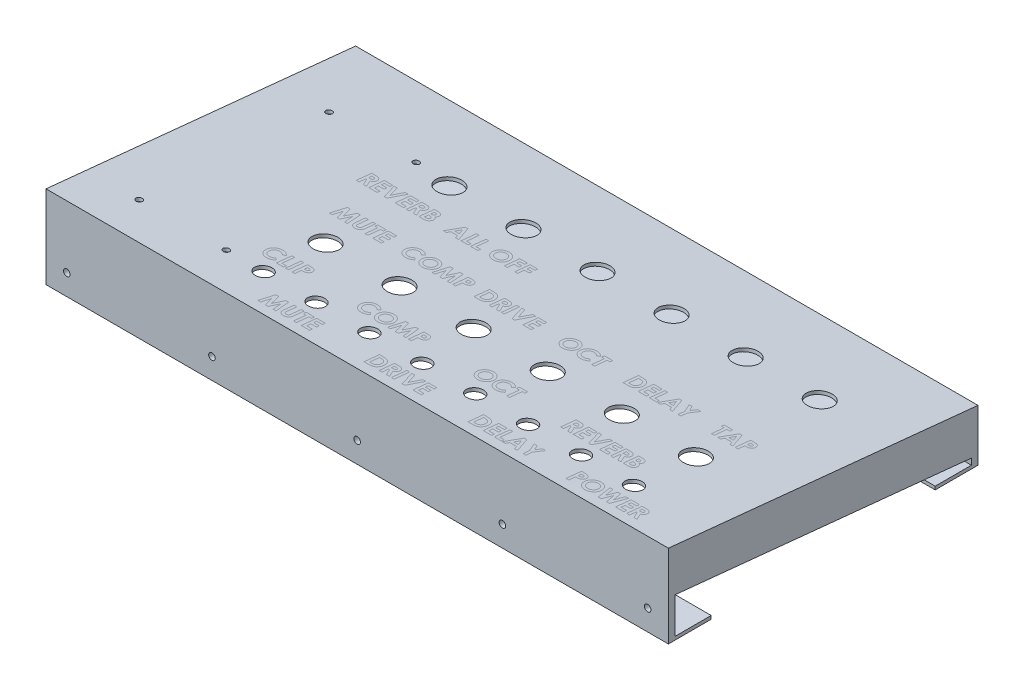
SolidWorks part; units mm, degrees
ref_plane "Plan de face" through (0, 0, 0) normal (0, 0, 1) x (1, 0, 0)
ref_plane "Plan de dessus" through (0, 0, 0) normal (0, 1, 0) x (1, 0, 0)
ref_plane "Plan de droite" through (0, 0, 0) normal (1, 0, 0) x (0, 0, -1)
sketch "Esquisse1" plane through (0, 0, 0) normal (1, 0, 0) x (0, 0, -1)
  line L0 (-26.398, -24.4282) -> (-26.398, 15.5718)
  line L1 (-26.398, 15.5718) -> (122.8501, 0.5718)
  line L2 (122.8501, 0.5718) -> (122.8501, -24.4282)
  line L3 (122.8501, -24.4282) -> (121.2626, -24.4282)
  line L4 (121.2626, -24.4282) -> (121.2626, -0.8641)
  line L5 (121.2626, -0.8641) -> (-24.8105, 13.8168)
  line L6 (-24.8105, 13.8168) -> (-24.8105, -24.4282)
  line L7 (-24.8105, -24.4282) -> (-26.398, -24.4282)
  line L8 (110.6669, 0.2008) -> (110.8256, 1.7803) construction
  dimension "D1" = 1.5875
  dimension "D2" = 40
  dimension "D3" = 25
  dimension "D4" = 150
extrude "Boss.-Extru.1" add sketch "Esquisse1" along normal blind 300
sketch "Esquisse3" plane through (0, 0, 24.8105) normal (0, 0, -1) x (-1, 0, 0)
  line L0 (-300, -24.4282) -> (-300, 13.8168) construction
  line L1 (-300, -5.3782) -> (0, -5.3782)
  line L2 (-300, -5.3782) -> (-300, -24.4282)
  line L3 (-300, -24.4282) -> (0, -24.4282)
  line L4 (0, -5.3782) -> (0, -24.4282)
  line L5 (-300, -24.4282) -> (0, -24.4282) construction
  line L6 (0, -24.4282) -> (0, 13.8168) construction
  dimension "D1" = 19.05
extrude "Boss.-Extru.2" add sketch "Esquisse3" along normal blind 1.5875
sketch "Esquisse4" plane through (0, 0, 23.223) normal (0, 0, -1) x (-1, 0, 0)
  line L0 (-300, -5.3782) -> (-300, -24.4282) construction
  line L1 (-300, -22.8407) -> (0, -22.8407)
  line L2 (-300, -22.8407) -> (-300, -24.4282)
  line L3 (-300, -24.4282) -> (0, -24.4282)
  line L4 (0, -22.8407) -> (0, -24.4282)
  line L5 (-300, -24.4282) -> (0, -24.4282) construction
  line L6 (0, -24.4282) -> (0, -5.3782) construction
  dimension "D1" = 1.5875
extrude "Boss.-Extru.3" add sketch "Esquisse4" along normal blind 17.4625
sketch "Esquisse5" plane through (0, 0, -121.2626) normal (0, 0, 1) x (1, 0, 0)
  line L0 (300, -24.4282) -> (0, -24.4282) construction
  line L1 (0, -5.3782) -> (300, -5.3782)
  line L2 (0, -5.3782) -> (0, -24.4282)
  line L3 (0, -24.4282) -> (300, -24.4282)
  line L4 (300, -5.3782) -> (300, -24.4282)
  line L5 (300, -0.8641) -> (300, -24.4282) construction
  line L6 (0, -0.8641) -> (0, -24.4282) construction
  dimension "D1" = 19.05
extrude "Boss.-Extru.4" add sketch "Esquisse5" along normal blind 1.5875
sketch "Esquisse6" plane through (0, 0, -119.6751) normal (0, 0, 1) x (1, 0, 0)
  line L0 (0, -5.3782) -> (0, -24.4282) construction
  line L1 (0, -22.8407) -> (300, -22.8407)
  line L2 (0, -22.8407) -> (0, -24.4282)
  line L3 (0, -24.4282) -> (300, -24.4282)
  line L4 (300, -22.8407) -> (300, -24.4282)
  dimension "D1" = 1.5875
extrude "Boss.-Extru.5" add sketch "Esquisse6" along normal blind 17.4625
sketch "Esquisse7" plane through (300, 0, 0) normal (1, 0, 0) x (0, 0, -1)
  line L0 (-24.8105, 13.8168) -> (-24.8105, 12.2213)
  line L1 (-24.8105, -5.3782) -> (-24.8105, 13.8168) construction
  line L2 (-24.8105, 12.2213) -> (121.2626, -2.4596)
  line L4 (121.2626, -2.4596) -> (121.2626, -0.8641)
  line L5 (121.2626, -0.8641) -> (-24.8105, 13.8168)
  dimension "D1" = 1.5875
extrude "Boss.-Extru.6" add sketch "Esquisse7" against normal blind 19.05
sketch "Esquisse8" plane through (300, 0, 0) normal (1, 0, 0) x (0, 0, -1)
  line L0 (-24.8105, 12.2213) -> (121.2626, -2.4596)
  line L1 (121.2626, -2.4596) -> (121.2626, -5.3782)
  line L2 (121.2626, -5.3782) -> (119.6751, -5.3782)
  line L3 (119.6751, -5.3782) -> (119.6751, -19.8505)
  line L4 (119.6751, -22.8407) -> (119.6751, -5.3782) construction
  line L5 (119.6751, -19.8505) -> (-24.8105, -5.3292)
  line L6 (-24.8105, -5.3782) -> (-24.8105, 12.2213) construction
  line L7 (-24.8105, -5.3292) -> (-24.8105, 12.2213)
  dimension "D1" = 17.4625
extrude "Boss.-Extru.7" add sketch "Esquisse8" against normal blind 1.5875
sketch "Esquisse9" plane through (0, 0, 0) normal (-1, 0, 0) x (0, 0, 1)
  line L0 (-121.2626, -0.8641) -> (24.8105, 13.8168)
  line L1 (24.8105, 13.8168) -> (24.8105, 12.2213)
  line L2 (24.8105, -5.3782) -> (24.8105, 13.8168) construction
  line L3 (24.8105, 12.2213) -> (-121.2626, -2.4596)
  line L4 (-121.2626, -0.8641) -> (-121.2626, -5.3782) construction
  line L5 (-121.2626, -2.4596) -> (-121.2626, -0.8641)
  dimension "D1" = 1.5875
extrude "Boss.-Extru.8" add sketch "Esquisse9" against normal blind 19.05 separate body
sketch "Esquisse11" plane through (0, 0, 0) normal (-1, 0, 0) x (0, 0, 1)
  line L0 (-121.2626, -2.4596) -> (-121.2626, -5.3782)
  line L1 (-121.2626, -5.3782) -> (-119.6751, -5.3782)
  line L2 (-119.6751, -5.3782) -> (-119.6751, -19.8505)
  line L3 (-119.6751, -5.3782) -> (-119.6751, -22.8407) construction
  line L4 (-119.6751, -19.8505) -> (24.8105, -5.3292)
  line L5 (24.8105, -5.3782) -> (24.8105, 13.8168) construction
  line L6 (24.8105, -5.3292) -> (24.8105, 12.2213)
  line L7 (24.8105, 12.2213) -> (-121.2626, -2.4596)
  dimension "D1" = 17.4625
extrude "Boss.-Extru.9" add sketch "Esquisse11" against normal blind 1.5875
sketch "Esquisse12" plane through (0, 0, -122.8501) normal (0, 0, -1) x (-1, 0, 0)
  line L1 (-300, -24.4282) -> (0, -24.4282) construction
  line L2 (-300, -24.4282) -> (-300, 0.5718) construction
  line L3 (0, -24.4282) -> (0, 0.5718) construction
  line L4 (-290, -14.4282) -> (-150, -14.4282) construction
  line L5 (-150, -14.4282) -> (-10, -14.4282) construction
  circle A0 centre (-290, -14.4282) radius 1.5875
  circle A1 centre (-150, -14.4282) radius 1.5875
  circle A2 centre (-10, -14.4282) radius 1.5875
  circle A3 centre (-220, -14.4282) radius 1.5875
  circle A4 centre (-80, -14.4282) radius 1.5875
  point P15 (-150, -24.4282)
  point P18 (-80, -14.4282)
  point P20 (-220, -14.4282)
  dimension "D1" = 3.175
  dimension "D2" = 10
  dimension "D3" = 10
  dimension "D4" = 10
extrude "Enlèv. mat.-Extru.1" cut sketch "Esquisse12" against normal through all
sketch "Esquisse13" plane through (0, 12.7896, -1.2854) normal (0, 0.995, -0.1) x (1, 0, 0)
  line L1 (300, -27.8228) -> (0, -27.8228) construction
  line L2 (0, 122.1772) -> (0, -27.8228) construction
  circle A0 centre (263.5, -7.8228) radius 4
  circle A1 centre (238, -7.8228) radius 4
  circle A2 centre (212.5, -7.8228) radius 4
  circle A3 centre (187, -7.8228) radius 4
  circle A4 centre (161.5, -7.8228) radius 4
  circle A5 centre (136, -7.8228) radius 4
  circle A6 centre (110.5, -7.8228) radius 4
  circle A7 centre (85, -7.8228) radius 4
  circle A8 centre (263.5, 22.1772) radius 6
  circle A9 centre (227.8, 22.1772) radius 6
  circle A10 centre (192.1, 22.1772) radius 6
  circle A11 centre (156.4, 22.1772) radius 6
  circle A12 centre (120.7, 22.1772) radius 6
  circle A13 centre (85, 22.1772) radius 6
  circle A14 centre (227.8, 82.1772) radius 6
  circle A15 centre (192.1, 82.1772) radius 6
  circle A16 centre (156.4, 82.1772) radius 6
  circle A17 centre (120.7, 82.1772) radius 6
  circle A18 centre (85, 82.1772) radius 6
  circle A19 centre (263.5, 82.1772) radius 6
  circle A20 centre (67, -7.8228) radius 1.5
  circle A21 centre (25, -7.8228) radius 1.5
  circle A22 centre (67, 84.1772) radius 1.5
  circle A23 centre (25, 84.1772) radius 1.5
  dimension "D1" = 8
  dimension "D5" = 12
  dimension "D6" = 6
  dimension "D10" = 3
  dimension "D3" = 85
  dimension "D4" = 20
  dimension "D8" = 85
  dimension "D9" = 50
  dimension "D11" = 42
  dimension "D12" = 92
  dimension "D13" = 25
  dimension "D14" = 20
  dimension "D2" = 8
  dimension "D7" = 2
extrude "Enlèv. mat.-Extru.2" cut sketch "Esquisse13" against normal up to next
sketch "Esquisse14" plane through (0, 12.7896, -1.2854) normal (0, 0.995, -0.1) x (1, 0, 0)
  circle A0 centre (85, -7.8228) radius 4 construction
  circle A1 centre (85, 22.1772) radius 6 construction
  circle A2 centre (85, 82.1772) radius 6 construction
  text T0 "<b>CLIP</b>" font "Century Gothic" height 7.5
  text T1 "<b>MUTE</b>" font "Century Gothic" height 7.5
  text T2 "<b>COMP</b>" font "Century Gothic" height 7.5
  text T3 "<b>DRIVE</b>" font "Century Gothic" height 7.5
  text T4 "<b>OCT</b>" font "Century Gothic" height 7.5
  text T5 "<b>DELAY</b>" font "Century Gothic" height 7.5
  text T6 "<b>REVERB</b>" font "Century Gothic" height 7.5
  text T7 "<b>POWER</b>" font "Century Gothic" height 7.5
  text T8 "<b>MUTE</b>" font "Century Gothic" height 7.5
  text T9 "<b>COMP</b>" font "Century Gothic" height 7.5
  text T10 "<b>DRIVE</b>" font "Century Gothic" height 7.5
  text T11 "<b>OCT</b>" font "Century Gothic" height 7.5
  text T12 "<b>DELAY</b>" font "Century Gothic" height 7.5
  text T13 "<b>TAP</b>" font "Century Gothic" height 7.5
  text T14 "<b>REVERB</b>" font "Century Gothic" height 7.5
  text T15 "<b>ALL OFF</b>" font "Century Gothic" height 7.5
  point P1 (80.2328, -1.8154)
  point P2 (77.1037, -0.8975)
  point P4 (117.2069, 0)
  point P5 (105.3674, -0.8975)
  point P6 (100.4771, -0.8975)
  point P7 (74.0972, -0.8975)
  point P9 (131.5897, 0)
  point P10 (130.9784, -0.8975)
  point P11 (71.6439, -0.5818)
  point P13 (164.3759, -0.5818)
  point P14 (0, 0)
  point P15 (0, 0)
  point P16 (74.7573, -0.6409)
  point P17 (103.1441, -19.5709)
  point P18 (99.6432, -22.897)
  point P19 (98.0317, -22.1122)
  point P20 (96.9037, -22.2668)
  point P21 (123.8003, -0.5818)
  point P22 (120.3008, -0.5818)
  point P23 (152.5446, -22.2668)
  point P24 (0, 0)
  point P25 (147.7978, -21.8542)
  point P28 (146.1782, -22.8228)
  point P29 (147.46, -22.8228)
  point P31 (178.6372, -0.3228)
  point P32 (177.544, -0.3228)
  point P33 (176.4449, -0.3228)
  point P35 (199.8109, -22.8228)
  point P36 (197.5844, -22.8228)
  point P38 (227.248, -0.3228)
  point P39 (0, 0)
  point P40 (222.795, -0.3228)
  point P41 (219.8263, -0.3228)
  point P43 (249.6558, -22.8228)
  point P44 (246.9294, -22.8228)
  point P45 (244.8336, -22.8228)
  point P47 (72.743, 39.2738)
  point P48 (71.7082, 38.1675)
  point P52 (108.6625, 37.1772)
  point P53 (105.9778, 37.1772)
  point P54 (104.4096, 37.1772)
  point P56 (145.5153, 37.1772)
  point P57 (142.8779, 37.1772)
  point P58 (140.7697, 37.1772)
  point P60 (180.3083, 37.1772)
  point P61 (179.7451, 37.1772)
  point P62 (181.2477, 37.1772)
  point P63 (179.4784, 37.1772)
  point P64 (181.6196, 37.1772)
  point P65 (180.0788, 37.1772)
  point P67 (219.8263, 39.0927)
  point P68 (214.8484, 37.1772)
  point P69 (211.2759, 37.1772)
  point P70 (212.6063, 37.1772)
  point P72 (250.0325, 37.1772)
  point P73 (256.8427, 37.1772)
  point P74 (254.6346, 37.1772)
  point P75 (255.66, 37.1772)
  point P76 (254.6251, 37.1772)
  point P80 (66.0353, 59.6772)
  point P82 (0, 0)
  point P83 (105.9523, 59.6772)
  point P84 (61.6199, 59.6772)
  point P85 (104.4096, 59.6772)
  dimension "D3" = 15
  dimension "D4" = 22.5
  dimension "D1" = 7.5
  dimension "D2" = 15
split line "Ligne de séparation1"
